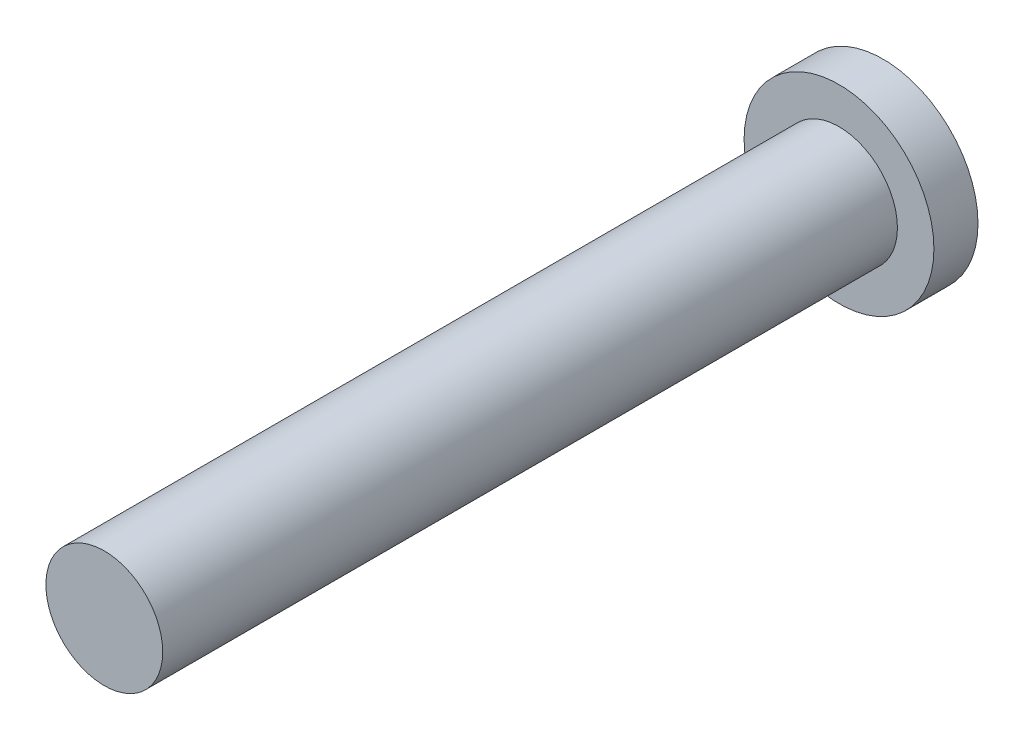
SolidWorks part; units mm, degrees
ref_plane "Front Plane" through (0, 0, 0) normal (0, 0, 1) x (1, 0, 0)
ref_plane "Top Plane" through (0, 0, 0) normal (0, 1, 0) x (1, 0, 0)
ref_plane "Right Plane" through (0, 0, 0) normal (1, 0, 0) x (0, 0, -1)
sketch "Sketch1" plane through (0, 0, 0) normal (0, 0, 1) x (1, 0, 0)
  circle A0 centre (0, 0) radius 2.5838
  dimension "D1" = 5.1675
extrude "Boss-Extrude1" add sketch "Sketch1" along normal blind 1.2
sketch "Sketch2" plane through (0, 0, 1.2) normal (0, 0, 1) x (1, 0, 0)
  circle A0 centre (0, 0) radius 1.59
  dimension "D1" = 3.18
extrude "Boss-Extrude2" add sketch "Sketch2" along normal blind 20
